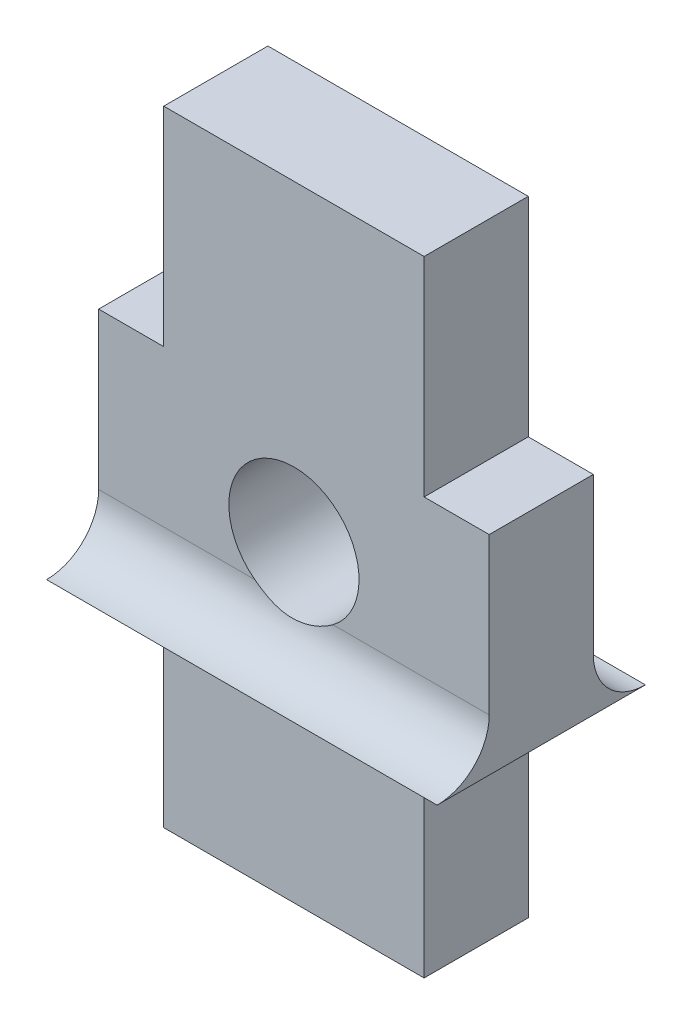
SolidWorks part; units mm, degrees
ref_plane "Front Plane" through (0, 0, 0) normal (0, 0, 1) x (1, 0, 0)
ref_plane "Top Plane" through (0, 0, 0) normal (0, 1, 0) x (1, 0, 0)
ref_plane "Right Plane" through (0, 0, 0) normal (1, 0, 0) x (0, 0, -1)
sketch "Sketch1" plane through (0, 0, 0) normal (0, 0, 1) x (1, 0, 0)
  line L0 (1952.1768, 1466.8841) -> (1957.1768, 1466.8841)
  line L1 (1952.1768, 1454.8841) -> (1957.1768, 1454.8841)
  line L3 (1957.1768, 1458.8841) -> (1957.1768, 1454.8841)
  line L4 (1957.1768, 1458.8841) -> (1958.4268, 1458.8841)
  line L5 (1958.4268, 1462.8841) -> (1958.4268, 1458.8841)
  line L6 (1957.1768, 1462.8841) -> (1957.1768, 1466.8841)
  line L7 (1957.1768, 1462.8841) -> (1958.4268, 1462.8841)
  line L37 (1952.1768, 1458.8841) -> (1950.9268, 1458.8841)
  line L40 (1952.1768, 1458.8841) -> (1952.1768, 1454.8841)
  line L127 (1952.1768, 1462.8841) -> (1950.9268, 1462.8841)
  line L130 (1952.1768, 1462.8841) -> (1952.1768, 1466.8841)
  line L131 (1950.9268, 1462.8841) -> (1950.9268, 1458.8841)
  circle A82 centre (1954.6768, 1460.8841) radius 1.25
  dimension "D1" = 2.5
  dimension "D2" = 1950.9268
  dimension "D3" = 1954.6768
  dimension "D4" = 1957.1768
  dimension "D5" = 1454.8841
  dimension "D6" = 1458.8841
  dimension "D7" = 1460.8841
extrude "Boss-Extrude1" add sketch "Sketch1" along normal blind 2
sketch "Sketch2" plane through (1950.9268, 0, 0) normal (-1, 0, 0) x (0, 0, 1)
  line L0 (1, 1454.8841) -> (1, 1461.8841) construction
  line L1 (2, 1458.8841) -> (2, 1459.8841)
  line L2 (2, 1458.8841) -> (3, 1458.8841)
  line L3 (0, 1458.8841) -> (-1, 1458.8841)
  line L4 (0, 1458.8841) -> (0, 1459.8841)
  arc A0 (2, 1459.8841) -> (3, 1458.8841) centre (3, 1459.8841) ccw
  arc A1 (0, 1459.8841) -> (-1, 1458.8841) centre (-1, 1459.8841) cw
  dimension "D1" = 1
  dimension "D2" = 1
  dimension "D3" = 4
  dimension "D4" = 1
  dimension "D5" = 4
  dimension "D6" = 2
extrude "Boss-Extrude2" add sketch "Sketch2" against normal up to surface (7.5 mm away) up to face at (1958.4268, 1460.8841, 1)
sketch "Sketch3" plane through (0, 0, 2) normal (0, 0, 1) x (1, 0, 0)
  circle A0 centre (1954.6768, 1460.8841) radius 1.25
  dimension "D1" = 2.5
extrude "Cut-Extrude1" cut sketch "Sketch3" against normal through all both and the other way through all
